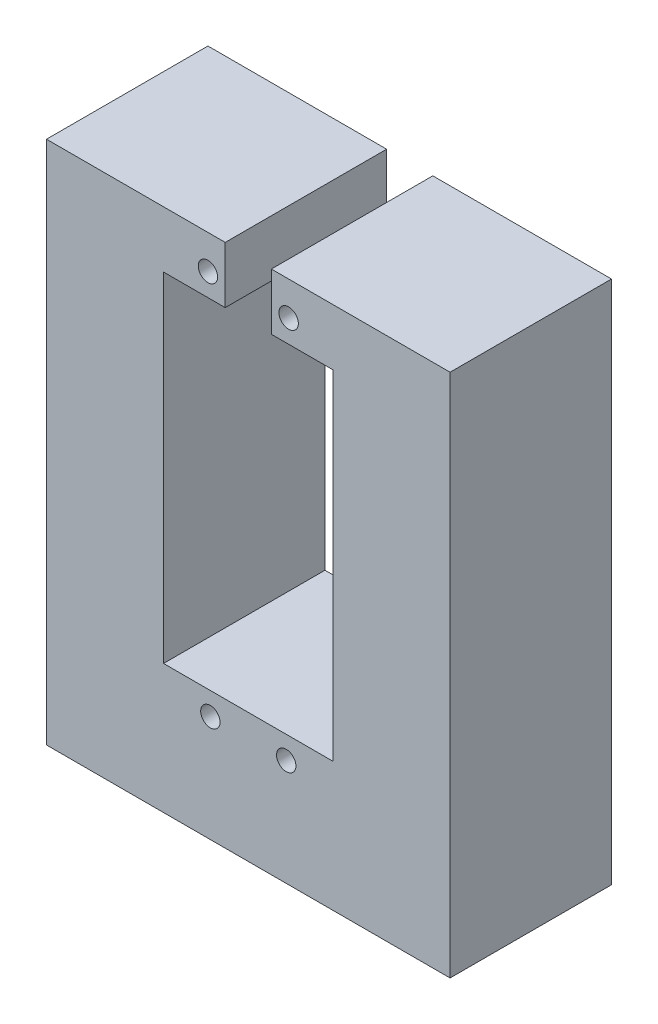
SolidWorks part; units mm, degrees
ref_plane "前基準面" through (0, 0, 0) normal (0, 0, 1) x (1, 0, 0)
ref_plane "上基準面" through (0, 0, 0) normal (0, 1, 0) x (1, 0, 0)
ref_plane "右基準面" through (0, 0, 0) normal (1, 0, 0) x (0, 0, -1)
sketch "草圖1" plane through (0, 0, 0) normal (0, 0, 1) x (1, 0, 0)
  line L0 (-22.9167, 0) -> (27.0833, 0)
  line L1 (2.0833, 0) -> (2.0833, 65) construction
  line L2 (-22.9167, 0) -> (-22.9167, 65)
  line L3 (27.0833, 0) -> (27.0833, 65)
  line L4 (27.0833, 65) -> (-22.9167, 65)
  dimension "D1" = 50
  dimension "D2" = 65
extrude "Boss-Extrude1" add sketch "草圖1" along normal blind 20
sketch "Sketch11" plane through (0, 0, 0) normal (0, 0, 1) x (1, 0, 0)
  line L0 (2.0833, 65) -> (2.0833, 0) construction
  line L1 (27.0833, 65) -> (-22.9167, 65) construction
  line L2 (-22.9167, 0) -> (27.0833, 0) construction
  line L3 (4.9423, 65) -> (-0.7756, 65)
  line L4 (-0.7756, 65) -> (-0.7756, 58)
  line L5 (-0.7756, 58) -> (-8.4167, 58)
  line L6 (-8.4167, 58) -> (-8.4167, 16)
  line L7 (-8.4167, 16) -> (12.5833, 16)
  line L8 (12.5833, 58) -> (12.5833, 16)
  line L9 (4.9423, 58) -> (12.5833, 58)
  line L10 (4.9423, 65) -> (4.9423, 58)
  circle A0 centre (-2.9167, 60.81) radius 1.2
  circle A1 centre (-2.6167, 13.19) radius 1.2
  circle A2 centre (6.7833, 13.19) radius 1.2
  circle A3 centre (7.0833, 60.81) radius 1.2
  point P12 (2.0833, 16)
  dimension "D4" = 2.4
  dimension "D5" = 2.4
  dimension "D1" = 42
  dimension "D2" = 7
  dimension "D3" = 21
  dimension "D6" = 2.81
  dimension "D7" = 5.5
  dimension "D8" = 5.8
  dimension "D9" = 2.81
  dimension "D10" = 7.6411
extrude "Cut-Extrude1" cut sketch "Sketch11" along normal blind 28
sketch "Sketch12" plane through (0, 0, 0) normal (0, 1, 0) x (1, 0, 0)
  circle A0 centre (-15.2327, -9.9189) radius 7
  circle A1 centre (18.7673, -9.9189) radius 7
  dimension "D2" = 14
  dimension "D3" = 14
  dimension "D1" = 34
extrude "Cut-Extrude2" cut sketch "Sketch12" along normal blind 15
